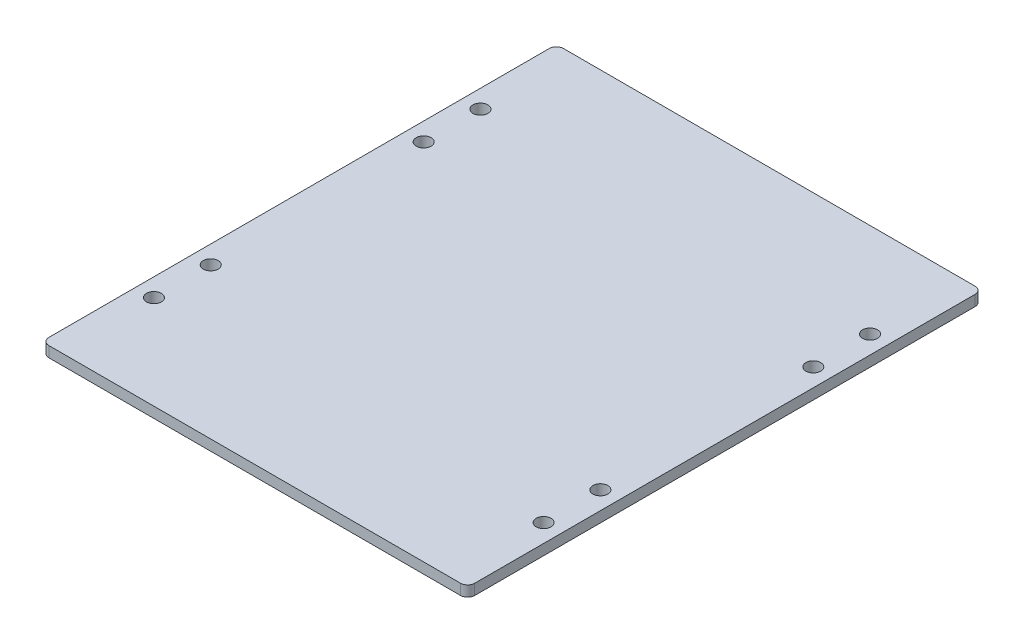
SolidWorks part; units mm, degrees
ref_plane "Front Plane" through (0, 0, 0) normal (0, 0, 1) x (1, 0, 0)
ref_plane "Top Plane" through (0, 0, 0) normal (0, 1, 0) x (1, 0, 0)
ref_plane "Right Plane" through (0, 0, 0) normal (1, 0, 0) x (0, 0, -1)
sketch "Sketch1" plane through (0, 0, 0) normal (0, 1, 0) x (1, 0, 0)
  line L0 (0, 145) -> (120, 0) construction
  line L1 (0, 0) -> (120, 0)
  line L2 (0, 0) -> (0, 145)
  line L3 (0, 145) -> (120, 145)
  line L4 (120, 0) -> (120, 145)
  dimension "length" = 145
  dimension "width" = 120
  dimension "D1" = 188.2153
extrude "Boss-Extrude1" add sketch "Sketch1" along normal blind 3
sketch "Sketch2" plane through (0, 3, 3) normal (0, 1, 0) x (1, 0, 0)
  line L0 (5.1, 105.5) -> (114.9, 105.5) construction
  line L5 (5.1, 121.5) -> (114.9, 121.5) construction
  line L6 (5.1, 121.5) -> (5.1, 29.5) construction
  line L7 (5.1, 29.5) -> (114.9, 29.5) construction
  line L8 (114.9, 121.5) -> (114.9, 29.5) construction
  line L9 (114.9, 45.5) -> (5.1, 45.5) construction
  line L16 (120, 148) -> (0, 148) construction
  line L17 (0, 148) -> (0, 3) construction
  circle A0 centre (5.1, 121.5) radius 2.1
  circle A1 centre (5.1, 105.5) radius 2.1
  circle A2 centre (5.1, 45.5) radius 2.1
  circle A3 centre (5.1, 29.5) radius 2.1
  circle A4 centre (114.9, 29.5) radius 2.1
  circle A5 centre (114.9, 45.5) radius 2.1
  circle A6 centre (114.9, 105.5) radius 2.1
  circle A7 centre (114.9, 121.5) radius 2.1
  point P2 (60, 148)
  point P3 (60, 121.5)
  point P15 (0, 75.5)
  point P16 (5.1, 75.5)
  dimension "D2" = 4.2
  dimension "D3" = 16
  dimension "D1" = 16
  dimension "D4" = 3
  dimension "D5" = 92
extrude "Cut-Extrude1" cut sketch "Sketch2" against normal through all
fillet "Fillet1" radius 2 4 edges at (0, 1.5, -145) (120, 1.5, -145) (120, 1.5, 0) (0, 1.5, 0)
equation "\"width\"= 24"
equation "\"thk\"= 3"
equation "\"holesize\"= 4.2"
equation "\"holedistance\"= ( 20 + 12 ) / 2"
equation "\"threaded_hole\"= 3.9"
equation "\"fillet_radius\"= 2"
equation "\"ground_clearance\"= 25"
equation "\"tire_thk\"= 3"
equation "\"innerwheel_diam\" = \"wheel_diam\"-2*\"tire_thk\""
equation "\"innerwheel_thk\"= 8"
equation "\"wheel_diam\"= 2*(\"width\"/2+\"ground_clearance\")"
equation "\"coloursensor_holesize\"= 2.65"
equation "\"D1@Boss-Extrude1\"=\"thk\""
equation "\"D3@Sketch2\"=\"holedistance\""
equation "\"D1@Sketch2\"=\"holedistance\""
equation "\"D2@Sketch2\"=\"holesize\""
equation "\"D1@Fillet1\"=\"fillet_radius\""
equation "\"D5@Sketch2\"=\"length@Sketch1\"-53"
equation "\"hole_to_edge\" = 4"
